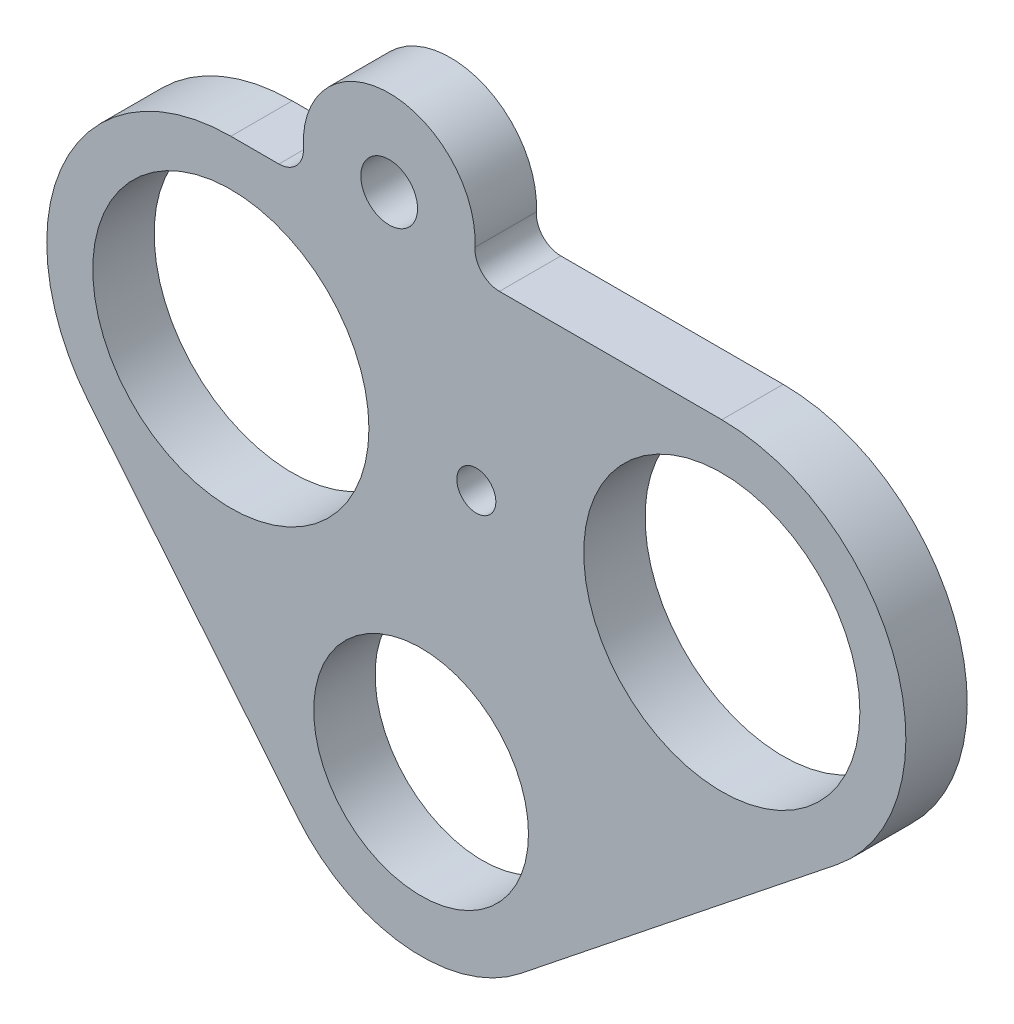
SolidWorks part; units mm, degrees
material "1060 Alloy"
ref_plane "Front Plane" through (0, 0, 0) normal (0, 0, 1) x (1, 0, 0)
ref_plane "Top Plane" through (0, 0, 0) normal (0, 1, 0) x (1, 0, 0)
ref_plane "Right Plane" through (0, 0, 0) normal (1, 0, 0) x (0, 0, -1)
sketch "Sketch1" plane through (0, 0, 0) normal (0, 0, 1) x (1, 0, 0)
  line L0 (-19.685, 47.1268) -> (31.115, 47.1268)
  line L1 (42.9965, 13.1861) -> (10.2973, -12.9052)
  line L2 (-12.7792, -10.4533) -> (-34.4303, 16.0153)
  line L3 (-19.685, 28.0768) -> (31.115, 28.0768) construction
  arc A0 (10.2973, -12.9052) -> (-12.7792, -10.4533) centre (0, 0) cw
  arc A1 (31.115, 47.1268) -> (42.9965, 13.1861) centre (31.115, 28.0768) cw
  arc A2 (-19.685, 47.1268) -> (-34.4303, 16.0153) centre (-19.685, 28.0768) ccw
  arc A3 (5.0017, 47.1268) -> (-11.6057, 47.1268) centre (-3.302, 50.3018) ccw
  circle A4 centre (-3.302, 50.3018) radius 2.9337
  point P10 (-59.8792, 47.1268)
  dimension "D1" = 16.51
  dimension "D2" = 50.8
  dimension "D3" = 34.29
  dimension "D5" = 19.05
  dimension "D6" = 19.05
  dimension "D7" = 8.89
  dimension "D9" = 5.8674
  dimension "D4" = 41.91
  dimension "D8" = 3.175
  dimension "D10" = 3.302
extrude "Boss-Extrude1" add sketch "Sketch1" along normal blind 6.35 contours L0 A3 | L0 A2 L2 A0 L1 A1
hole_wizard "1 (1) Diameter Hole1" positions "Sketch8" profile "Sketch9" hole size "1" standard "ANSI Inch"
sketch "Sketch8" plane through (0, 0, 6.35) normal (0, 0, 1) x (1, 0, 0)
  arc A0 (-19.685, 47.1268) -> (-34.4303, 16.0153) centre (-19.685, 28.0768) ccw construction
  arc A1 (42.9965, 13.1861) -> (31.115, 47.1268) centre (31.115, 28.0768) ccw construction
  point P0 (-19.685, 28.0768)
  point P2 (31.115, 28.0768)
sketch "Sketch9" plane through (-19.685, 28.0768, 6.35) normal (1, 0, 0) x (0, -1, 0)
  line L0 (0, 0) -> (0, 33.9848)
  line L1 (0, 33.9848) -> (14.2875, 25.4)
  line L2 (14.2875, 25.4) -> (14.2875, 0)
  line L5 (14.2875, 0) -> (0, 0)
  line L10 (0, 33.9848) -> (-14.2875, 25.4) construction
  line L11 (0, -6.35) -> (0, 107.95) construction
  dimension "Hole Dia." = 28.575
  dimension "Hole Depth" = 25.4
  dimension "Drill Angle" = 118
hole_wizard "7/8 (0.875) Diameter Hole1" positions "Sketch10" profile "Sketch11" hole size "7/8" standard "ANSI Inch"
sketch "Sketch10" plane through (0, 0, 6.35) normal (0, 0, 1) x (1, 0, 0)
  arc A0 (-12.7792, -10.4533) -> (10.2973, -12.9052) centre (0, 0) ccw construction
  point P0 (0, 0)
sketch "Sketch11" plane through (0, 0, 6.35) normal (1, 0, 0) x (0, -1, 0)
  line L0 (0, 0) -> (0, 32.0771)
  line L1 (0, 32.0771) -> (11.1125, 25.4)
  line L2 (11.1125, 25.4) -> (11.1125, 0)
  line L5 (11.1125, 0) -> (0, 0)
  line L10 (0, 32.0771) -> (-11.1125, 25.4) construction
  line L11 (0, -6.35) -> (0, 107.95) construction
  dimension "Hole Dia." = 22.225
  dimension "Hole Depth" = 25.4
  dimension "Drill Angle" = 118
hole_wizard "Tap Drill for #10-32 Tap1" positions "Sketch12" profile "Sketch13" hole size "#10-32" standard "ANSI Inch" end condition through all
sketch "Sketch12" plane through (0, 0, 6.35) normal (0, 0, 1) x (1, 0, 0)
  line L0 (-19.685, 28.0768) -> (31.115, 28.0768) construction
  point P0 (5.715, 28.0768)
  point P3 (5.715, 28.0768)
sketch "Sketch13" plane through (5.715, 28.0768, 6.35) normal (1, 0, 0) x (0, -1, 0)
  line L0 (0, 0) -> (0, 6.35)
  line L1 (0, 6.35) -> (2.0193, 6.35)
  line L2 (2.0193, 6.35) -> (2.0193, 0)
  line L5 (2.0193, 0) -> (0, 0)
  line L11 (0, -6.35) -> (0, 107.95) construction
  dimension "Thru Hole Dia." = 4.0386
  dimension "Thru Hole Depth" = 6.35
fillet "Fillet1" radius 2.54 2 edges at (-11.6057, 47.1268, 3.175) (5.0017, 47.1268, 3.175)
